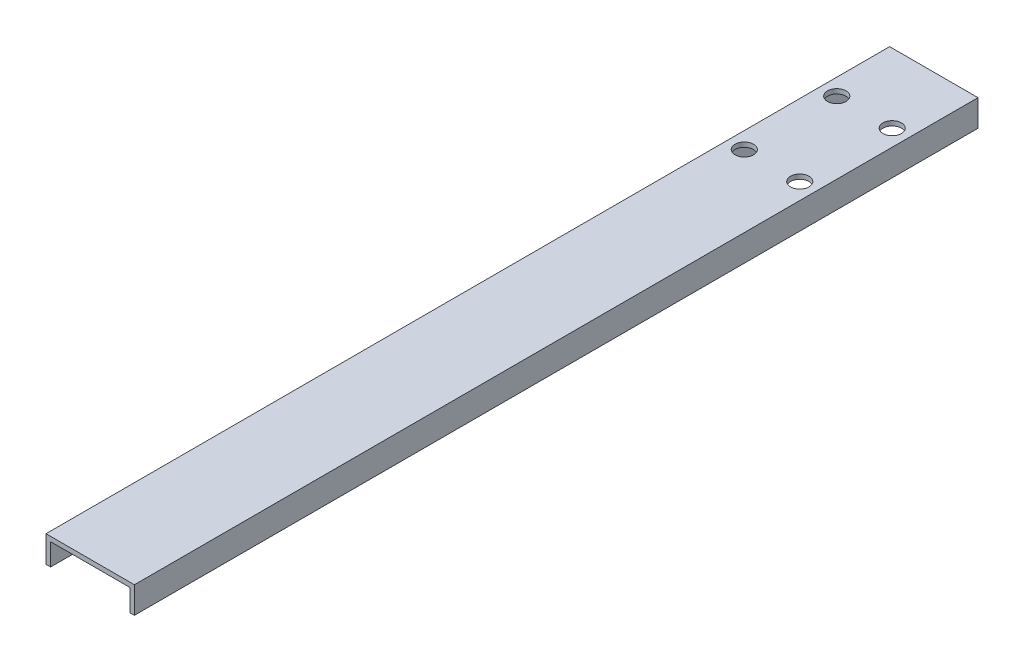
SolidWorks part; units mm, degrees
ref_plane "Front Plane" through (0, 0, 0) normal (0, 0, 1) x (1, 0, 0)
ref_plane "Top Plane" through (0, 0, 0) normal (0, 1, 0) x (1, 0, 0)
ref_plane "Right Plane" through (0, 0, 0) normal (1, 0, 0) x (0, 0, -1)
sketch "Sketch1" plane through (0, 0, 0) normal (0, 0, 1) x (1, 0, 0)
  line L0 (0, 0) -> (0, 7.2898)
  line L1 (0, 7.2898) -> (24.2824, 7.2898)
  line L2 (24.2824, 7.2898) -> (24.2824, 0)
  line L3 (24.2824, 0) -> (23.0124, 0)
  line L4 (23.0124, 0) -> (23.0124, 6.0198)
  line L5 (23.0124, 6.0198) -> (1.27, 6.0198)
  line L6 (1.27, 6.0198) -> (1.27, 0)
  line L7 (1.27, 0) -> (0, 0)
  point P3 (12.1412, 7.2898)
  dimension "D1" = 24.2824
  dimension "D2" = 7.2898
  dimension "D3" = 1.27
  dimension "D4" = 1.27
  dimension "D5" = 1.27
extrude "Boss-Extrude1" add sketch "Sketch1" along normal blind 231.775
ref_plane "Plane1" through (12.1412, 0, 0) normal (1, 0, 0) x (0, 0, -1)
sketch "Sketch2" plane through (0, 7.2898, 0) normal (0, 1, 0) x (1, 0, 0)
  line L0 (12.1412, 0) -> (12.1412, -231.775) construction
  line L1 (24.2824, 0) -> (0, 0) construction
  line L2 (24.2824, -231.775) -> (0, -231.775) construction
  line L4 (4.5212, -19.05) -> (19.7612, -19.05) construction
  line L5 (4.5212, -19.05) -> (4.5212, -44.45) construction
  line L6 (4.5212, -44.45) -> (19.7612, -44.45) construction
  line L7 (19.7612, -19.05) -> (19.7612, -44.45) construction
  line L8 (4.5212, -19.05) -> (19.7612, -44.45) construction
  line L9 (4.5212, -44.45) -> (19.7612, -19.05) construction
  circle A0 centre (4.5212, -19.05) radius 2.54
  circle A1 centre (19.7612, -19.05) radius 2.54
  circle A2 centre (19.7612, -44.45) radius 2.54
  circle A3 centre (4.5212, -44.45) radius 2.54
  point P6 (12.1412, -31.75)
  dimension "D4" = 5.08
  dimension "D1" = 15.24
  dimension "D2" = 25.4
  dimension "D3" = 31.75
extrude "Cut-Extrude1" cut sketch "Sketch2" against normal through all
